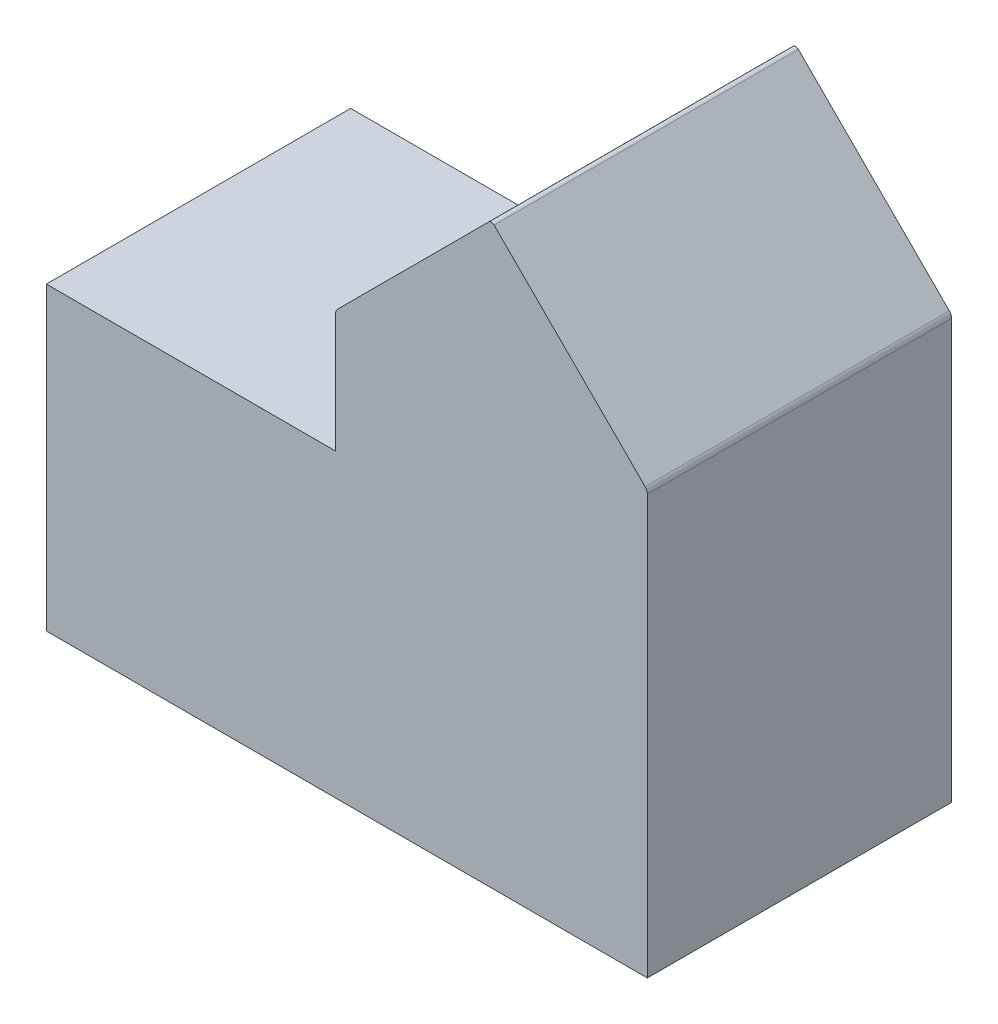
SolidWorks part; units mm, degrees
ref_plane "Front Plane" through (0, 0, 0) normal (0, 0, 1) x (1, 0, 0)
ref_plane "Top Plane" through (0, 0, 0) normal (0, 1, 0) x (1, 0, 0)
ref_plane "Right Plane" through (0, 0, 0) normal (1, 0, 0) x (0, 0, -1)
sketch "Sketch1" plane through (0, 0, 0) normal (0, 0, 1) x (1, 0, 0)
  line L0 (10.033, 5.0165) -> (10.033, 9.0805)
  line L1 (-10.033, -5.0165) -> (10.033, -5.0165)
  line L2 (-10.033, -5.0165) -> (-10.033, 5.0165)
  line L3 (-10.033, 5.0165) -> (10.033, 5.0165)
  line L4 (10.033, -5.0165) -> (10.033, 5.0165)
  line L5 (-10.033, -5.0165) -> (10.033, 5.0165) construction
  line L6 (-10.033, 5.0165) -> (10.033, -5.0165) construction
  line L7 (10.033, 9.0805) -> (4.826, 14.2875)
  line L8 (4.826, 14.2875) -> (-0.381, 9.0805)
  line L9 (-0.381, 9.0805) -> (-0.381, 5.0165)
  point P0 (0, 0)
  dimension "D1" = 20.066
  dimension "D2" = 225
  dimension "D3" = 9.652
  dimension "D4" = 19.304
  dimension "D5" = 10.033
extrude "Boss-Extrude1" add sketch "Sketch1" along normal mid plane 10.16 contours L8 L9 L3 L0 L7 | L1 L4 L3 L2
fillet "Fillet1" radius 0.254 2 edges at (-0.381, 9.0805, 0) (10.033, 9.0805, 0)
fillet "Fillet2" radius 0.127 1 edges at (4.826, 14.2875, 0)
